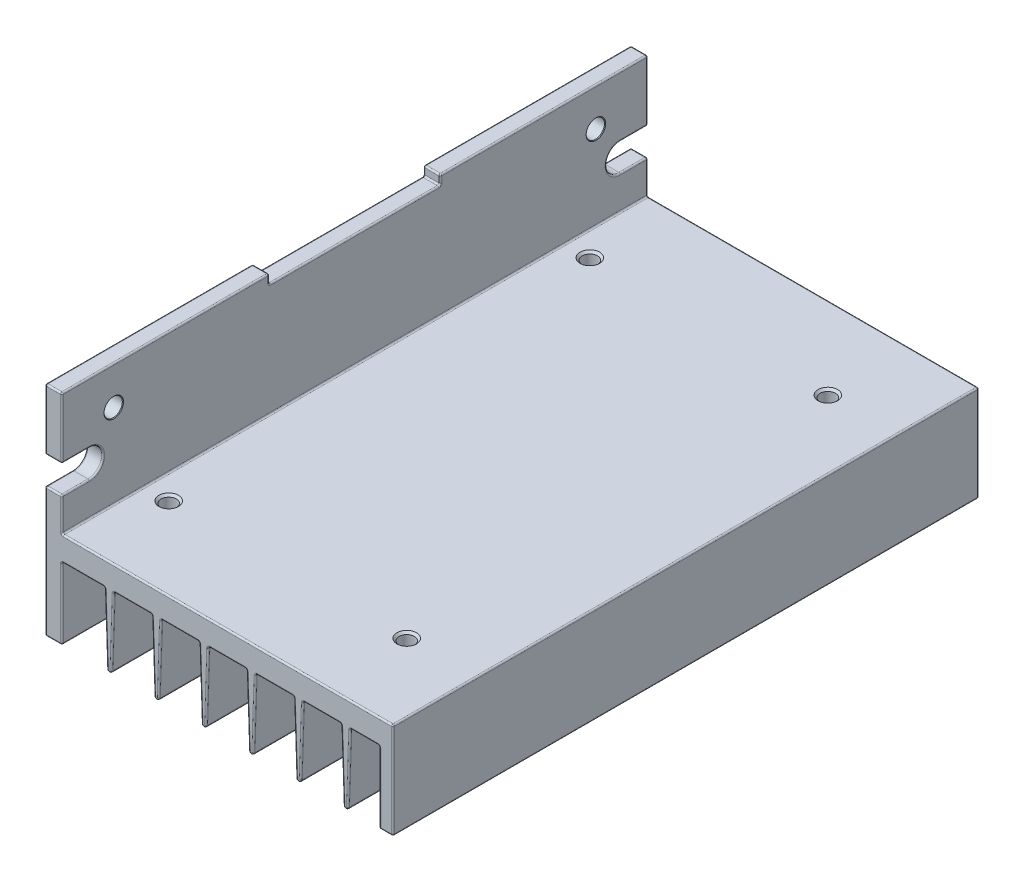
SolidWorks part; units mm, degrees
material "AlMgSi0.5-T4 (6060)"
ref_plane "Front Plane" through (0, 0, 0) normal (0, 0, 1) x (1, 0, 0)
ref_plane "Top Plane" through (0, 0, 0) normal (0, 1, 0) x (1, 0, 0)
ref_plane "Right Plane" through (0, 0, 0) normal (1, 0, 0) x (0, 0, -1)
sketch "Body Profile Sketch" plane through (0, 0, 0) normal (0, 0, 1) x (1, 0, 0)
  line L43 (0.25, 0) -> (54, 0)
  line L44 (54.25, -0.25) -> (54.25, -15.5)
  line L50 (54, -15.75) -> (52.25, -15.75)
  line L51 (52, -15.5) -> (52, -4.25)
  line L52 (51.75, -4) -> (47.4919, -4)
  line L53 (0, -4.25) -> (0, -15.5)
  line L54 (-0.25, -15.75) -> (-2.5, -15.75)
  line L55 (-2.75, -15.5) -> (-2.75, 19.75)
  line L56 (-2.5, 20) -> (-0.25, 20)
  line L57 (0, 19.75) -> (0, 0.25)
  line L58 (8.492, -4.2418) -> (8.1248, -15.3873)
  line L59 (7.008, -4.2418) -> (7.3752, -15.3873)
  line L60 (7.75, -4) -> (7.75, -15.75) construction
  line L61 (6.7581, -4) -> (0.25, -4)
  line L62 (8.5, -4) -> (7, -4) construction
  line L63 (16.242, -4.2418) -> (15.8748, -15.3873)
  line L64 (16.25, -4) -> (14.75, -4) construction
  line L65 (15.5, -4) -> (15.5, -15.75) construction
  line L66 (14.758, -4.2418) -> (15.1252, -15.3873)
  line L67 (23.992, -4.2418) -> (23.6248, -15.3873)
  line L68 (24, -4) -> (22.5, -4) construction
  line L69 (23.25, -4) -> (23.25, -15.75) construction
  line L70 (22.508, -4.2418) -> (22.8752, -15.3873)
  line L71 (31.742, -4.2418) -> (31.3748, -15.3873)
  line L72 (31.75, -4) -> (30.25, -4) construction
  line L73 (31, -4) -> (31, -15.75) construction
  line L74 (30.258, -4.2418) -> (30.6252, -15.3873)
  line L75 (39.492, -4.2418) -> (39.1248, -15.3873)
  line L76 (39.5, -4) -> (38, -4) construction
  line L77 (38.75, -4) -> (38.75, -15.75) construction
  line L78 (38.008, -4.2418) -> (38.3752, -15.3873)
  line L79 (47.242, -4.2418) -> (46.8748, -15.3873)
  line L80 (47.25, -4) -> (45.75, -4) construction
  line L81 (46.5, -4) -> (46.5, -15.75) construction
  line L82 (45.758, -4.2418) -> (46.1252, -15.3873)
  line L83 (14.5081, -4) -> (8.7419, -4)
  line L84 (22.2581, -4) -> (16.4919, -4)
  line L85 (30.0081, -4) -> (24.2419, -4)
  line L86 (37.7581, -4) -> (31.9919, -4)
  line L87 (45.5081, -4) -> (39.7419, -4)
  arc A28 (7.3752, -15.3873) -> (8.1248, -15.3873) centre (7.75, -15.375) ccw
  arc A29 (-0.25, 20) -> (0, 19.75) centre (-0.25, 19.75) cw
  arc A30 (-2.75, 19.75) -> (-2.5, 20) centre (-2.5, 19.75) cw
  arc A31 (0.25, 0) -> (0, 0.25) centre (0.25, 0.25) cw
  arc A32 (-2.5, -15.75) -> (-2.75, -15.5) centre (-2.5, -15.5) cw
  arc A33 (0, -15.5) -> (-0.25, -15.75) centre (-0.25, -15.5) cw
  arc A34 (0.25, -4) -> (0, -4.25) centre (0.25, -4.25) ccw
  arc A35 (7.008, -4.2418) -> (6.7581, -4) centre (6.7581, -4.25) ccw
  arc A36 (8.492, -4.2418) -> (8.7419, -4) centre (8.7419, -4.25) cw
  arc A37 (54, 0) -> (54.25, -0.25) centre (54, -0.25) cw
  arc A38 (52, -4.25) -> (51.75, -4) centre (51.75, -4.25) ccw
  arc A39 (54.25, -15.5) -> (54, -15.75) centre (54, -15.5) cw
  arc A40 (52.25, -15.75) -> (52, -15.5) centre (52.25, -15.5) cw
  arc A41 (16.242, -4.2418) -> (16.4919, -4) centre (16.4919, -4.25) cw
  arc A42 (15.1252, -15.3873) -> (15.8748, -15.3873) centre (15.5, -15.375) ccw
  arc A43 (14.758, -4.2418) -> (14.5081, -4) centre (14.5081, -4.25) ccw
  arc A44 (23.992, -4.2418) -> (24.2419, -4) centre (24.2419, -4.25) cw
  arc A45 (22.8752, -15.3873) -> (23.6248, -15.3873) centre (23.25, -15.375) ccw
  arc A46 (22.508, -4.2418) -> (22.2581, -4) centre (22.2581, -4.25) ccw
  arc A47 (31.742, -4.2418) -> (31.9919, -4) centre (31.9919, -4.25) cw
  arc A48 (30.6252, -15.3873) -> (31.3748, -15.3873) centre (31, -15.375) ccw
  arc A49 (30.258, -4.2418) -> (30.0081, -4) centre (30.0081, -4.25) ccw
  arc A50 (39.492, -4.2418) -> (39.7419, -4) centre (39.7419, -4.25) cw
  arc A51 (38.3752, -15.3873) -> (39.1248, -15.3873) centre (38.75, -15.375) ccw
  arc A52 (38.008, -4.2418) -> (37.7581, -4) centre (37.7581, -4.25) ccw
  arc A53 (47.242, -4.2418) -> (47.4919, -4) centre (47.4919, -4.25) cw
  arc A54 (46.1252, -15.3873) -> (46.8748, -15.3873) centre (46.5, -15.375) ccw
  arc A55 (45.758, -4.2418) -> (45.5081, -4) centre (45.5081, -4.25) ccw
  point P11 (7.75, -4)
  point P22 (-2.75, 20)
  point P25 (0, 0)
  point P28 (-2.75, -15.75)
  point P31 (0, -15.75)
  point P34 (0, -4)
  point P47 (54.25, -15.75)
  point P50 (52, -15.75)
  dimension "D7" = 0.375
  dimension "D8" = 1.5
  dimension "D10" = 0.25
  dimension "D11" = 6
  dimension "D1" = 57
  dimension "D2" = 2.25
  dimension "D3" = 4
  dimension "D4" = 2.75
  dimension "D5" = 11.75
  dimension "D6" = 35.75
  dimension "D9" = 7.75
  dimension "D12" = 7.75
extrude "Body" add sketch "Body Profile Sketch" along normal mid plane 96
sketch "Top Cut Out Sketch" plane through (0, 20, 0) normal (0, 1, 0) x (1, 0, 0)
  line L1 (14, -14) -> (-14, -14)
  line L2 (14, -14) -> (14, 14)
  line L3 (14, 14) -> (-14, 14)
  line L4 (-14, -14) -> (-14, 14)
  line L5 (14, -14) -> (-14, 14) construction
  line L6 (14, 14) -> (-14, -14) construction
  point P0 (0, 0)
  dimension "D1" = 28
extrude "Top Cut Out" cut sketch "Top Cut Out Sketch" against normal blind 1.5
sketch "Side Cut Out Sketch" plane through (0, 0, 0) normal (1, 0, 0) x (0, 0, -1)
  line L0 (48, 10) -> (43.5, 10)
  line L1 (48, 5.5) -> (43.5, 5.5)
  line L2 (48, 0.25) -> (48, 19.75) construction
  line L3 (0, 0) -> (0, 23.773) construction
  line L4 (-48, 10) -> (-43.5, 10)
  line L5 (-48, 5.5) -> (-43.5, 5.5)
  line L7 (48, 5.5) -> (48, 10)
  line L8 (-48, 5.5) -> (-48, 10)
  arc A0 (43.5, 10) -> (43.5, 5.5) centre (43.5, 7.75) ccw
  arc A1 (-43.5, 10) -> (-43.5, 5.5) centre (-43.5, 7.75) cw
  dimension "D1" = 87
  dimension "D3" = 2.25
  dimension "D2" = 7.75
extrude "Side Cut Out" cut sketch "Side Cut Out Sketch" against normal through all
hole_wizard "M3 Top Holes" positions "Sketch3" profile "Sketch4" tap size "M3" standard "ISO" end condition through all
sketch "Sketch3" plane through (0, 0, 0) normal (0, 1, 0) x (1, 0, 0)
  line L0 (43, 34.5) -> (4, -34.5) construction
  line L4 (0, -48) -> (0, 48) construction
  point P0 (43, 34.5)
  point P2 (43, -34.5)
  point P4 (4, -34.5)
  point P6 (4, 34.5)
  point P13 (23.5, 0)
  dimension "D1" = 69
  dimension "D2" = 39
  dimension "D3" = 43
sketch "Sketch4" plane through (43, 0, -34.5) normal (1, 0, 0) x (0, 0, 1)
  line L0 (0, 0) -> (0, 4)
  line L1 (0, 4) -> (1.6, 4)
  line L2 (1.25, 3.65) -> (1.25, 0.35)
  line L3 (1.25, 0.35) -> (1.6, 0)
  line L5 (1.6, 0) -> (0, 0)
  line L6 (-1.25, 0.35) -> (-1.6, 0) construction
  line L7 (1.6, 4) -> (1.25, 3.65)
  line L8 (-1.6, 4) -> (-1.25, 3.65) construction
  line L11 (0, -6.35) -> (0, 107.95) construction
  dimension "Thru Tap Drill Dia." = 2.5
  dimension "Thru Tap Drill Depth" = 4
  dimension "Near C'Sink Dia." = 3.2
  dimension "Near C'Sink Angle" = 90
  dimension "Far C'Sink Dia." = 3.2
  dimension "Far C'Sink Angle" = 90
cosmetic thread "Hole Thread1" parameters "D2"=3
cosmetic thread "Hole Thread2" parameters "D2"=3
cosmetic thread "Hole Thread3" parameters "D2"=3
cosmetic thread "Hole Thread4" parameters "D2"=3
hole_wizard "Ø3.0 Side Holes" positions "Sketch5" profile "Sketch6" hole size "Ø3.0" standard "ISO" end condition through all
sketch "Sketch5" plane through (0, 0, 0) normal (1, 0, 0) x (0, 0, -1)
  line L0 (-39.5, 13.75) -> (39.5, 13.75) construction
  point P0 (39.5, 13.75)
  point P2 (-39.5, 13.75)
  point P9 (0, 13.75)
  dimension "D1" = 79
  dimension "D2" = 13.75
sketch "Sketch6" plane through (0, 13.75, -39.5) normal (0, 1, 0) x (0, 0, -1)
  line L0 (0, 0) -> (0, 2.75)
  line L1 (0, 2.75) -> (1.6, 2.75)
  line L2 (1.5, 2.65) -> (1.5, 0.1)
  line L3 (1.5, 0.1) -> (1.6, 0)
  line L5 (1.6, 0) -> (0, 0)
  line L6 (-1.5, 0.1) -> (-1.6, 0) construction
  line L7 (1.6, 2.75) -> (1.5, 2.65)
  line L8 (-1.6, 2.75) -> (-1.5, 2.65) construction
  line L11 (0, -6.35) -> (0, 107.95) construction
  dimension "Thru Hole Dia." = 3
  dimension "Thru Hole Depth" = 2.75
  dimension "Near C'Sink Dia." = 3.2
  dimension "Near C'Sink Angle" = 90
  dimension "Far C'Sink Dia." = 3.2
  dimension "Far C'Sink Angle" = 90
fillet "Production Fillet" radius 0.25 124 edges at (-1.375, 20, -14) (-0.0732, 19.9268, -14) (-0.0732, 19.9268, 14) (-2.6768, 19.9268, 14) (0, 19.125, -14) (-2.75, 19.125, -14) (-2.75, 19.125, 14) (-2.75, 10, -45.75) (-2.75, 7.75, -41.25) (0, 10, -45.75) (0, 7.75, -41.25) (-2.75, 10, 45.75) (0, 7.75, 41.25) (0, 2.875, 48) (0.0732, 0.0732, 48) (27.125, 0, 48) (54.1768, -0.0732, 48) (54.25, -7.875, 48) (54.1768, -15.6768, 48) (53.125, -15.75, 48) (52.0732, -15.6768, 48) (52, -9.875, 48) (51.9268, -4.0732, 48) (49.6209, -4, 48) (47.3181, -4.0703, 48) (47.0584, -9.8146, 48) (46.5, -15.75, 48) (45.9416, -9.8146, 48) (42.625, -4, 48) (39.5681, -4.0703, 48) (39.3084, -9.8146, 48) (38.75, -15.75, 48) (37.9319, -4.0703, 48) (34.875, -4, 48) (31.8181, -4.0703, 48) (31.5584, -9.8146, 48) (31, -15.75, 48) (30.4416, -9.8146, 48) (30.1819, -4.0703, 48) (27.125, -4, 48) (24.0681, -4.0703, 48) (23.8084, -9.8146, 48) (23.25, -15.75, 48) (22.6916, -9.8146, 48) (22.4319, -4.0703, 48) (19.375, -4, 48) (16.3181, -4.0703, 48) (16.0584, -9.8146, 48) (15.5, -15.75, 48) (14.9416, -9.8146, 48) (14.6819, -4.0703, 48) (11.625, -4, 48) (8.3084, -9.8146, 48) (7.75, -15.75, 48) (7.1916, -9.8146, 48) (6.9319, -4.0703, 48) (0.0732, -4.0732, 48) (0, -9.875, 48) (-0.0732, -15.6768, 48) (-1.375, -15.75, 48) (-2.75, -5, -48) (-2.6768, -15.6768, -48) (-1.375, -15.75, -48) (0, -9.875, -48) (0.0732, -4.0732, -48) (3.5041, -4, -48) (7.1916, -9.8146, -48) (8.5681, -4.0703, -48) (11.625, -4, -48) (14.6819, -4.0703, -48) (14.9416, -9.8146, -48) (15.5, -15.75, -48) (16.0584, -9.8146, -48) (16.3181, -4.0703, -48) (19.375, -4, -48) (22.4319, -4.0703, -48) (22.6916, -9.8146, -48) (23.25, -15.75, -48) (23.8084, -9.8146, -48) (24.0681, -4.0703, -48) (27.125, -4, -48) (31.8181, -4.0703, -48) (34.875, -4, -48) (38.1916, -9.8146, -48) (38.75, -15.75, -48) (39.3084, -9.8146, -48) (39.5681, -4.0703, -48) (42.625, -4, -48) (45.6819, -4.0703, -48) (45.9416, -9.8146, -48) (46.5, -15.75, -48) (47.0584, -9.8146, -48) (47.3181, -4.0703, -48) (49.6209, -4, -48) (51.9268, -4.0732, -48) (52, -9.875, -48) (52.0732, -15.6768, -48) (53.125, -15.75, -48) (54.25, -7.875, -48) (54.1768, -0.0732, -48) (27.125, 0, -48) (0.0732, 0.0732, -48) (0, 2.875, -48) (-2.75, 5.5, -45.75) (-1.375, 5.5, -48) (0, 5.5, -45.75) (-0.0732, 19.9268, -48) (-1.375, 20, -48) (-2.6768, 19.9268, -48) (-2.75, 14.875, -48) (-1.375, 10, -48) (-1.375, 5.5, 48) (0, 5.5, 45.75) (-2.6768, 19.9268, 48) (-1.375, 20, 48) (-0.0732, 19.9268, 48) (0, 14.875, 48) (-1.375, 10, 48) (-2.75, 14.875, 48) (-1.375, 18.5, -14) (0, 18.5, 0) (-1.375, 18.5, 14) (-2.75, 18.5, 0) (-2.75, -5, 48)
